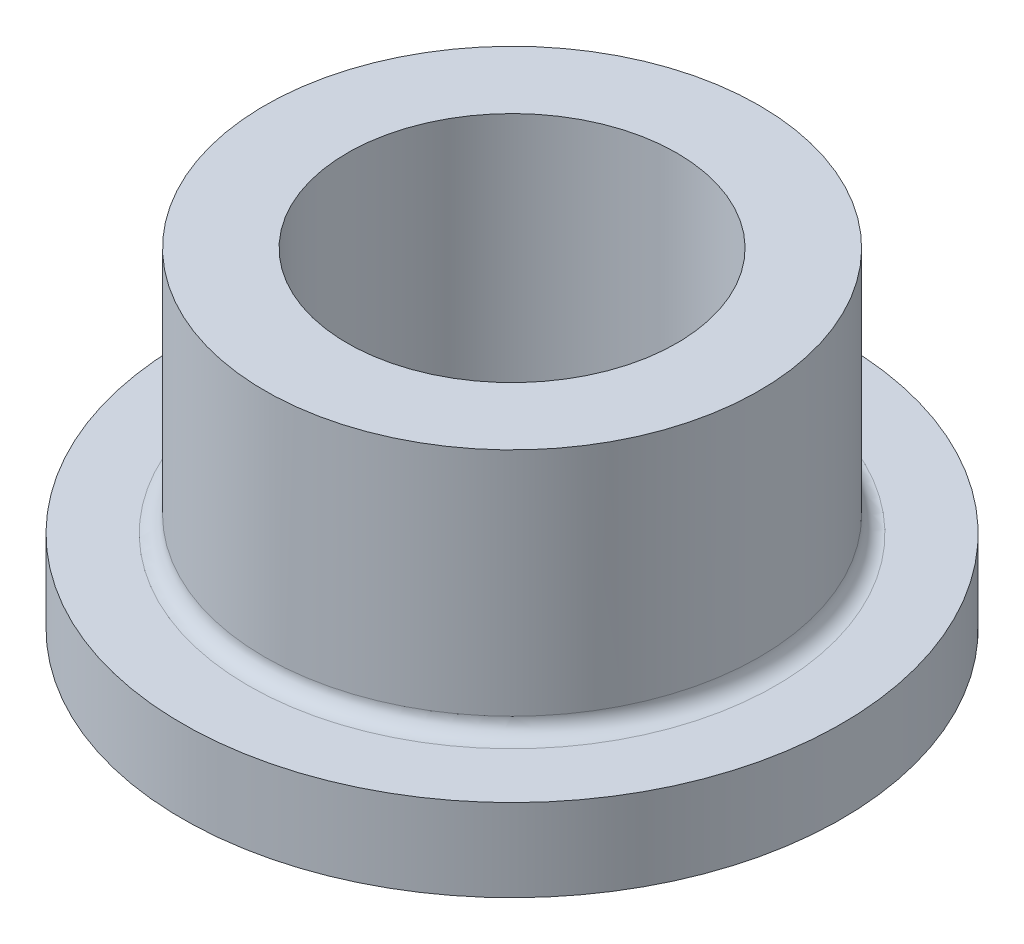
SolidWorks part; units mm, degrees
material "PMMA"
ref_plane "Front Plane" through (0, 0, 0) normal (0, 0, 1) x (1, 0, 0)
ref_plane "Top Plane" through (0, 0, 0) normal (0, 1, 0) x (1, 0, 0)
ref_plane "Right Plane" through (0, 0, 0) normal (1, 0, 0) x (0, 0, -1)
sketch "Sketch1" plane through (0, 0, 0) normal (1, 0, 0) x (0, 0, -1)
  line L0 (0, 0) -> (0, 8) construction
  line L1 (4, 8) -> (4, 0)
  line L2 (4, 0) -> (8, 0)
  line L3 (8, 0) -> (8, 2)
  line L4 (8, 2) -> (6, 2)
  line L5 (4, 8) -> (6, 8)
  line L6 (6, 8) -> (6, 2)
  dimension "D1" = 8
  dimension "D2" = 4
  dimension "D3" = 6
  dimension "D4" = 2
  dimension "D5" = 8
revolve "Revolve1" add sketch "Sketch1" angle 360 about L0
fillet "Fillet1" radius 0.4 1 edges at (0, 2, -6)
